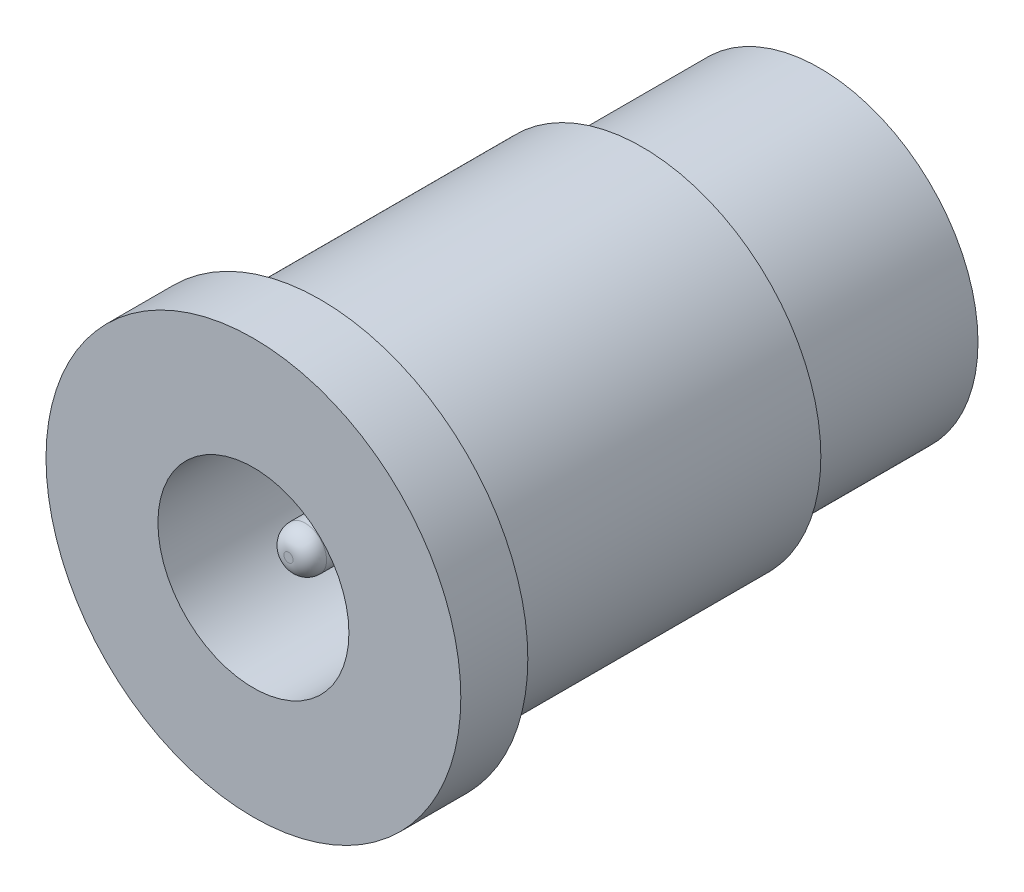
SolidWorks part; units mm, degrees
ref_plane "Front Plane" through (0, 0, 0) normal (0, 0, 1) x (1, 0, 0)
ref_plane "Top Plane" through (0, 0, 0) normal (0, 1, 0) x (1, 0, 0)
ref_plane "Right Plane" through (0, 0, 0) normal (1, 0, 0) x (0, 0, -1)
sketch "Sketch1" plane through (0, 0, 0) normal (1, 0, 0) x (0, 0, -1)
  line L0 (0, 2.85) -> (0, 6.19)
  line L1 (0, 6.19) -> (2, 6.19)
  line L2 (2, 6.19) -> (2, 5.335)
  line L3 (2, 5.335) -> (11.6, 5.335)
  line L4 (11.6, 5.335) -> (11.6, 4.725)
  line L5 (11.6, 4.725) -> (16.9, 4.725)
  line L6 (16.9, 4.725) -> (16.9, 0)
  line L7 (16.9, 0) -> (1.0468, 0)
  line L8 (1.0468, 0) -> (1.0468, 0.1372)
  line L9 (1.5468, 0.6372) -> (11.6, 0.6372)
  line L10 (11.6, 0.6372) -> (11.6, 2.85)
  line L11 (11.6, 2.85) -> (0, 2.85)
  line L12 (-5.0066, 0) -> (-3.0574, 0) construction
  arc A0 (1.0468, 0.1372) -> (1.5468, 0.6372) centre (1.5468, 0.1372) cw
  point P15 (0, 0)
  dimension "D8" = 0.5
  dimension "D1" = 12.38
  dimension "D2" = 10.67
  dimension "D3" = 9.45
  dimension "D4" = 5.7
  dimension "D5" = 2
  dimension "D6" = 5.3
  dimension "D7" = 16.9
revolve "Revolve1" add sketch "Sketch1" angle 360 about L12
